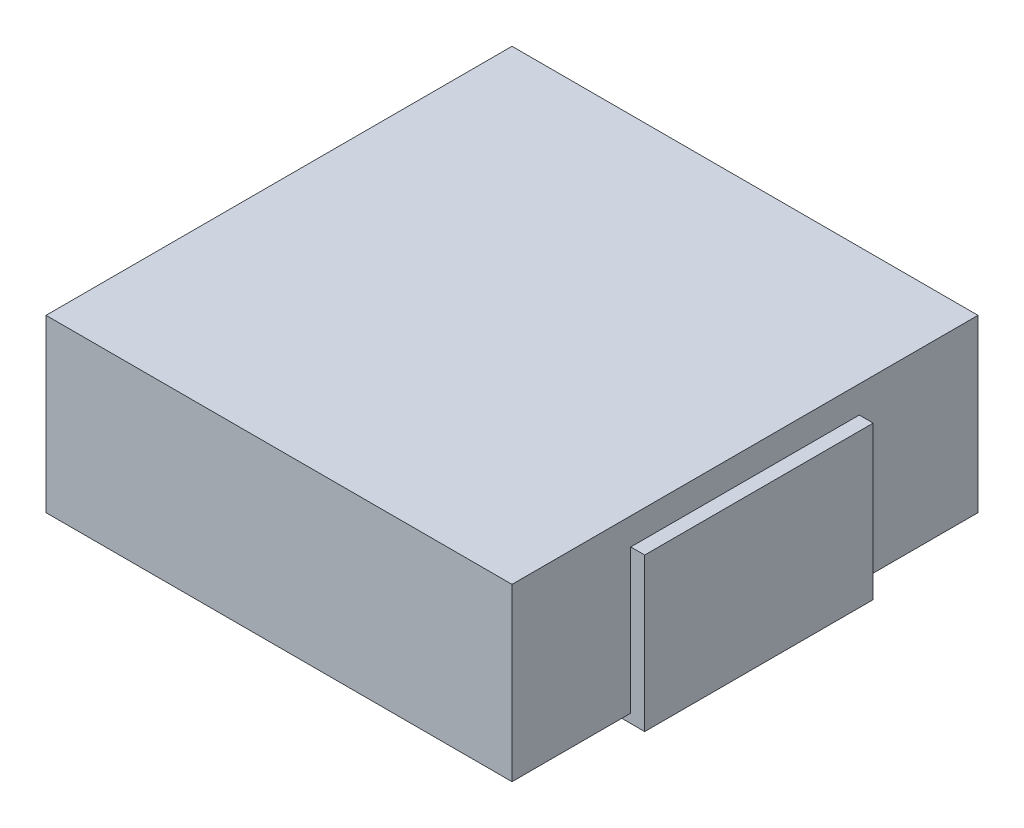
SolidWorks part; units mm, degrees
material "К270В2-II-08пс ГОСТ16523-97"
ref_plane "Спереди" through (0, 0, 0) normal (0, 0, 1) x (1, 0, 0)
ref_plane "Сверху" through (0, 0, 0) normal (0, 1, 0) x (1, 0, 0)
ref_plane "Справа" through (0, 0, 0) normal (1, 0, 0) x (0, 0, -1)
sketch "Эскиз1" plane through (0, 0, 0) normal (0, 1, 0) x (1, 0, 0)
  line L0 (0, 0) -> (2.59, 0) construction
  line L1 (-2.59, -2.59) -> (2.59, -2.59)
  line L2 (-2.59, -2.59) -> (-2.59, 2.59)
  line L3 (-2.59, 2.59) -> (2.59, 2.59)
  line L4 (2.59, -2.59) -> (2.59, 2.59)
  line L5 (-2.59, -2.59) -> (2.59, 2.59) construction
  line L6 (-2.59, 2.59) -> (2.59, -2.59) construction
  point P0 (0, 0)
  dimension "D1" = 5.18
  dimension "D2" = 5.18
extrude "Бобышка-Вытянуть1" add sketch "Эскиз1" along normal blind 1.9 from offset 0.1
sketch "Эскиз2" plane through (0, 0, 0) normal (0, 1, 0) x (1, 0, 0)
  line L0 (0, 0) -> (0, 2.59) construction
  line L1 (0, 0) -> (-2.59, 0) construction
  line L2 (2.59, 2.59) -> (-2.59, 2.59) construction
  line L3 (-2.745, -1.27) -> (-1.725, -1.27)
  line L4 (-2.745, -1.27) -> (-2.745, 1.27)
  line L5 (-2.745, 1.27) -> (-1.725, 1.27)
  line L6 (-1.725, -1.27) -> (-1.725, 1.27)
  line L7 (-2.745, -1.27) -> (-1.725, 1.27) construction
  line L8 (-2.745, 1.27) -> (-1.725, -1.27) construction
  line L9 (-2.59, 2.59) -> (-2.59, -2.59) construction
  line L10 (2.745, -1.27) -> (1.725, -1.27)
  line L11 (1.725, -1.27) -> (1.725, 1.27)
  line L12 (2.745, 1.27) -> (1.725, 1.27)
  line L13 (2.745, -1.27) -> (2.745, 1.27)
  point P3 (-2.235, 0)
  dimension "D1" = 2.745
  dimension "D2" = 2.54
  dimension "D3" = 1.02
  dimension "D4" = 0.155
  dimension "D5" = 5.49
extrude "Бобышка-Вытянуть2" add sketch "Эскиз2" along normal blind 1.7 separate body
